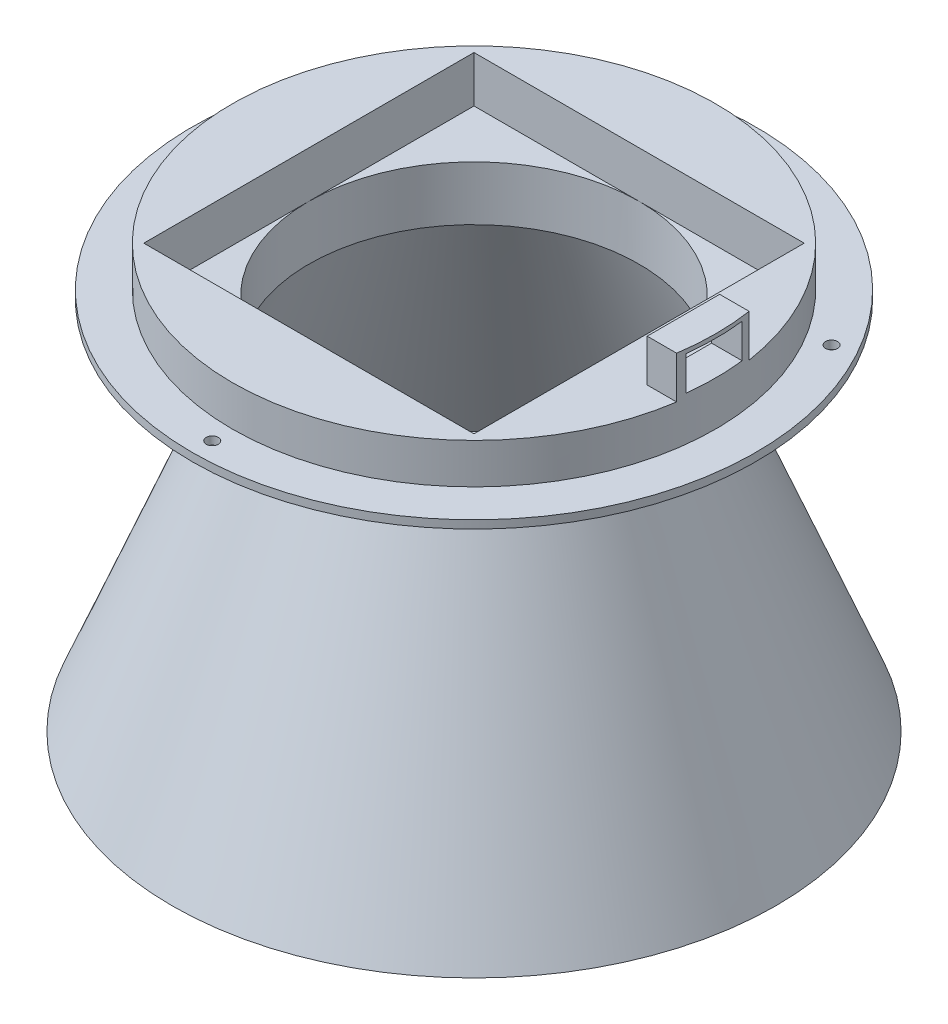
SolidWorks part; units mm, degrees
ref_plane "Alzado" through (0, 0, 0) normal (0, 0, 1) x (1, 0, 0)
ref_plane "Planta" through (0, 0, 0) normal (0, 1, 0) x (1, 0, 0)
ref_plane "Vista lateral" through (0, 0, 0) normal (1, 0, 0) x (0, 0, -1)
sketch "Croquis1" plane through (0, 0, 0) normal (0, 0, 1) x (1, 0, 0)
  line L0 (-67.9016, 46.9761) -> (-67.9016, 61.9761)
  line L1 (-69.9016, 46.9761) -> (-69.9016, -33.0239) construction
  line L2 (-67.9016, 46.9761) -> (14.0984, 46.9761) construction
  line L3 (-26.9016, 46.9761) -> (-26.9016, -33.0239) construction
  line L4 (-26.9016, -33.0239) -> (-101.9016, -33.0239) construction
  line L5 (-69.9016, 46.9761) -> (-101.9016, -33.0239)
  line L6 (-101.9016, -33.0239) -> (-99.9016, -33.0239)
  line L7 (-99.9016, -33.0239) -> (-67.9016, 46.9761)
  line L8 (-26.9016, 46.9761) -> (-26.9016, 61.9761) construction
  line L9 (-26.9016, 61.9761) -> (-86.9016, 61.9761) construction
  line L11 (-86.9016, 61.9761) -> (-96.9016, 61.9761)
  line L12 (-96.9016, 59.9761) -> (-86.9016, 59.9761)
  line L13 (-96.9016, 61.9761) -> (-96.9016, 59.9761)
  line L14 (-86.9016, 59.9761) -> (-69.9016, 46.9761)
  line L15 (-86.9016, 61.9761) -> (-86.9016, 71.9761)
  line L16 (-86.9016, 71.9761) -> (-67.9016, 71.9761)
  line L17 (-67.9016, 71.9761) -> (-67.9016, 61.9761)
  dimension "D1" = 19
  dimension "D2" = 10
revolve "Revolución1" add sketch "Croquis1" angle 360 about L3
sketch "Croquis2" plane through (0, 71.9761, 0) normal (0, 1, 0) x (1, 0, 0)
  line L1 (14.0984, -41) -> (-67.9016, -41)
  line L2 (14.0984, -41) -> (14.0984, 41)
  line L3 (14.0984, 41) -> (-67.9016, 41)
  line L4 (-67.9016, -41) -> (-67.9016, 41)
  line L5 (14.0984, -41) -> (-67.9016, 41) construction
  line L6 (14.0984, 41) -> (-67.9016, -41) construction
  point P0 (-26.9016, 0)
  dimension "D1" = 82
  dimension "D2" = 82
extrude "Cortar-Extruir1" cut sketch "Croquis2" against normal blind 11.5
sketch "Croquis3" plane through (0, 71.9761, 0) normal (0, 1, 0) x (1, 0, 0)
  line L0 (14.0984, -41) -> (14.0984, 41) construction
  line L3 (32.4195, 9) -> (25.0984, 9)
  line L4 (25.0984, 9) -> (25.0984, -9)
  line L5 (25.0984, -9) -> (32.4195, -9)
  arc A2 (32.4195, 9) -> (32.4195, -9) centre (-26.9016, 0) cw
extrude "Saliente-Extruir1" add sketch "Croquis3" along normal blind 10.5
sketch "Croquis4" plane through (25.0984, 0, 0) normal (-1, 0, 0) x (0, 0, 1)
  line L0 (-9, 71.9761) -> (9, 82.4761) construction
  line L1 (9, 82.4761) -> (9, 71.9761) construction
  line L2 (9, 71.9761) -> (-9, 82.4761) construction
  line L4 (-7, 81.4761) -> (7, 81.4761)
  line L5 (-7, 81.4761) -> (-7, 72.9761)
  line L6 (-7, 72.9761) -> (7, 72.9761)
  line L7 (7, 81.4761) -> (7, 72.9761)
  line L8 (-7, 81.4761) -> (7, 72.9761) construction
  line L9 (-7, 72.9761) -> (7, 81.4761) construction
  point P6 (0, 77.2261)
  dimension "D1" = 14
  dimension "D2" = 8.5
extrude "Cortar-Extruir2" cut sketch "Croquis4" against normal blind 10.5
sketch "Croquis5" plane through (0, 61.9761, 0) normal (0, 1, 0) x (1, 0, 0)
  line L0 (-26.9016, -70) -> (-26.9016, -60) construction
  line L1 (-26.9016, -70) -> (-26.9016, 70) construction
  line L2 (-26.9016, 0) -> (-35.8271, 0) construction
  circle A0 centre (-26.9016, 0) radius 70 construction
  circle A1 centre (-26.9016, 0) radius 60 construction
  circle A2 centre (-26.9016, -65) radius 1.5
  circle A3 centre (-83.1933, 32.5) radius 1.5
  circle A4 centre (29.39, 32.5) radius 1.5
  point P19 (-26.9016, 0)
  dimension "D1" = 3
extrude "Cortar-Extruir3" cut sketch "Croquis5" against normal blind 10
